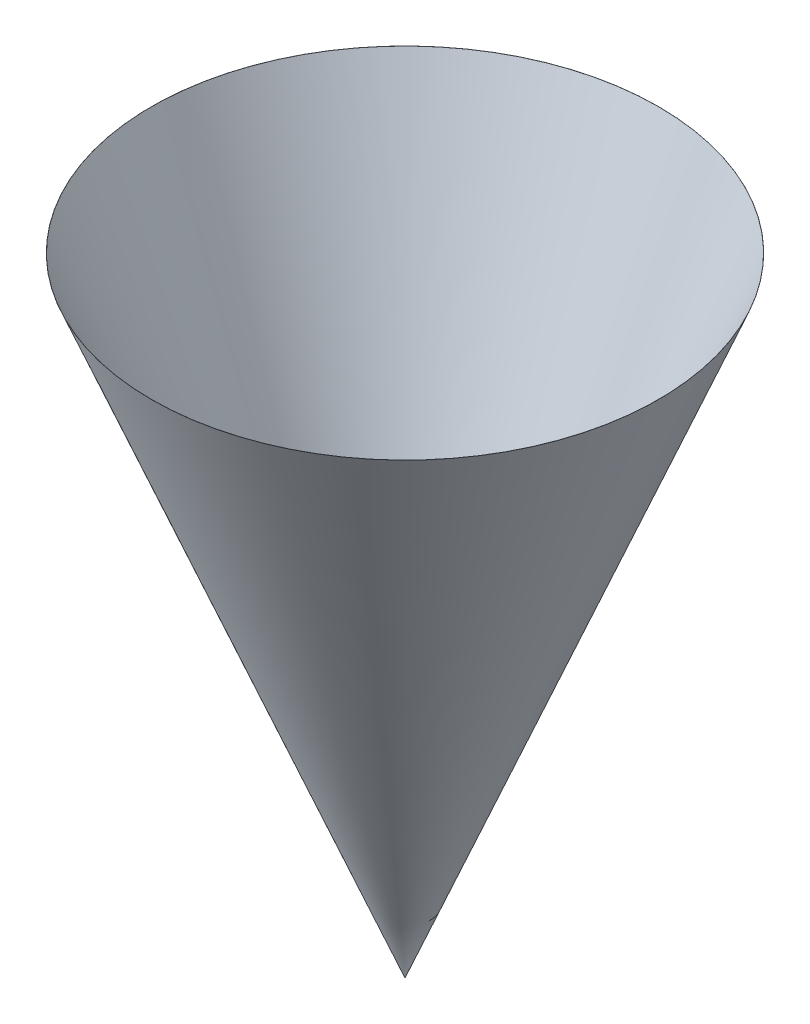
SolidWorks part; units mm, degrees
ref_plane "前视基准面" through (0, 0, 0) normal (0, 0, 1) x (1, 0, 0)
ref_plane "上视基准面" through (0, 0, 0) normal (0, 1, 0) x (1, 0, 0)
ref_plane "右视基准面" through (0, 0, 0) normal (1, 0, 0) x (0, 0, -1)
sketch "草图2" plane through (0, 0, 0) normal (1, 0, 0) x (0, 0, -1)
  line L0 (0, 0) -> (0, 27.0153) construction
  line L1 (0, 0) -> (32.3221, 80)
  line L2 (32.3221, 80) -> (32.3121, 80)
  line L3 (32.3121, 80) -> (0, 0.0248)
  line L4 (0, 0.0248) -> (0, 0)
  dimension "D1" = 22
  dimension "D2" = 0.01
  dimension "D3" = 80
revolve "旋转1" add sketch "草图2" angle 360 about L0
